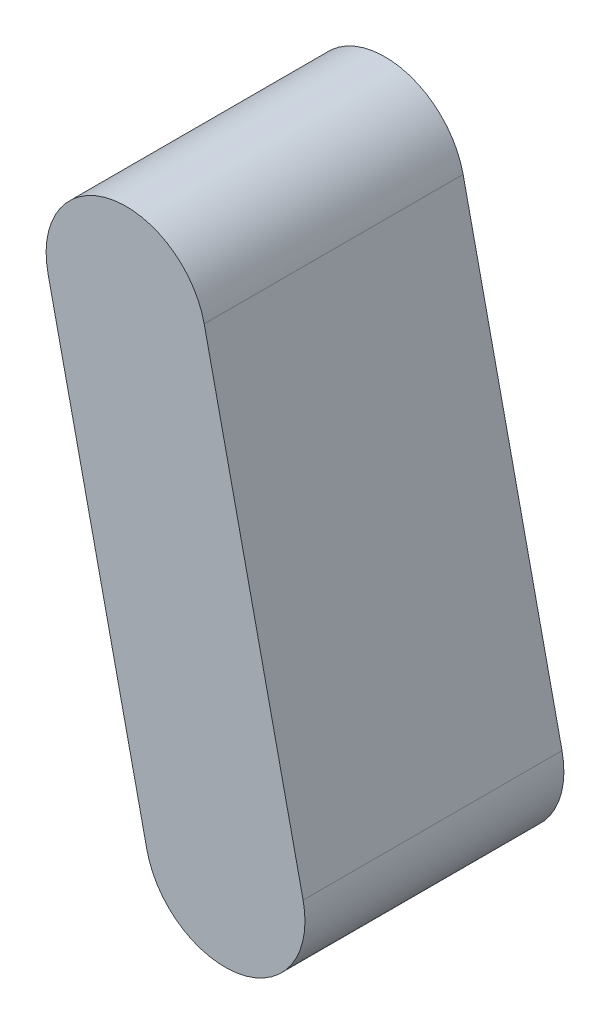
SolidWorks part; units mm, degrees
ref_plane "Front" through (0, 0, 0) normal (0, 0, 1) x (1, 0, 0)
ref_plane "Top" through (0, 0, 0) normal (0, 1, 0) x (1, 0, 0)
ref_plane "Right" through (0, 0, 0) normal (1, 0, 0) x (0, 0, -1)
sketch "Sketch1" plane through (0, 0, 0) normal (0, 0, 1) x (1, 0, 0)
  line L0 (-1958.4278, 191.2422) -> (-2002.0885, 389.6962) construction
  line L1 (-1958.4278, 191.2422) -> (-2002.0885, 389.6962)
  line L2 (-2036.5698, 382.1101) -> (-1992.9091, 183.6561)
  line L3 (-1967.6071, 397.2822) -> (-1923.9464, 198.8282)
  arc A0 (-1992.9091, 183.6561) -> (-1923.9464, 198.8282) centre (-1958.4278, 191.2422) ccw
  arc A1 (-1979.1892, 219.7987) -> (-1941.5315, 160.2417) centre (-1958.4278, 191.2422) ccw construction
  arc A2 (-2036.5698, 382.1101) -> (-1967.6071, 397.2822) centre (-2002.0885, 389.6962) cw
extrude "Boss-Extrude1" add sketch "Sketch1" against normal up to surface (114.3 mm away)
equation "\"mass\"= \"human weight@FS2-FR-HA-A-0001-V1, HUMAN ANALOG.Assembly\" * \"foot percent@FS2-FR-HA-A-0001-V1, HUMAN ANALOG.Assembly\" + \"shoe weight@FS2-FR-HA-A-0001-V1, HUMAN ANALOG.Assembly\""
